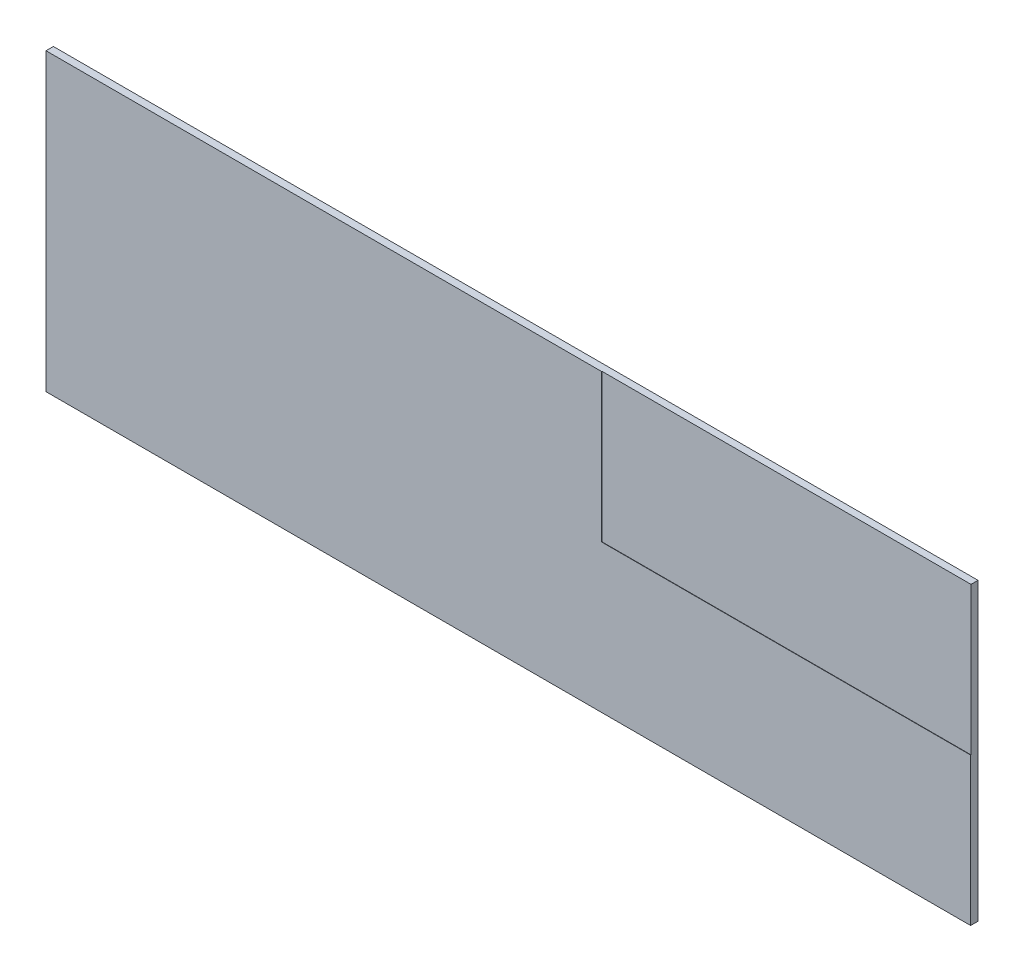
SolidWorks part; units mm, degrees
ref_plane "Alzado" through (0, 0, 0) normal (0, 0, 1) x (1, 0, 0)
ref_plane "Planta" through (0, 0, 0) normal (0, 1, 0) x (1, 0, 0)
ref_plane "Vista lateral" through (0, 0, 0) normal (1, 0, 0) x (0, 0, -1)
sketch "Croquis1" plane through (0, 0, 0) normal (0, 0, 1) x (1, 0, 0)
  line L1 (-12525, -4000) -> (12525, -4000)
  line L2 (-12525, -4000) -> (-12525, 4000)
  line L3 (-12525, 4000) -> (12525, 4000)
  line L4 (12525, -4000) -> (12525, 4000)
  line L5 (-12525, -4000) -> (12525, 4000) construction
  line L6 (-12525, 4000) -> (12525, -4000) construction
  point P0 (0, 0)
  dimension "D1" = 8000
  dimension "D2" = 25050
extrude "Saliente-Extruir1" add sketch "Croquis1" along normal blind 200
sketch "Croquis2" plane through (0, 0, 200) normal (0, 0, 1) x (1, 0, 0)
  line L0 (12525, 4000) -> (12525, 0)
  line L1 (12525, -4000) -> (12525, 4000) construction
  line L2 (12525, 4000) -> (2525, 4000)
  line L3 (12525, 4000) -> (-12525, 4000) construction
  line L4 (2525, 4000) -> (2525, 0)
  line L5 (2525, 0) -> (12525, 0)
  dimension "D1" = 4000
  dimension "D2" = 10000
extrude "Cortar-Extruir1" cut sketch "Croquis2" against normal blind 10
